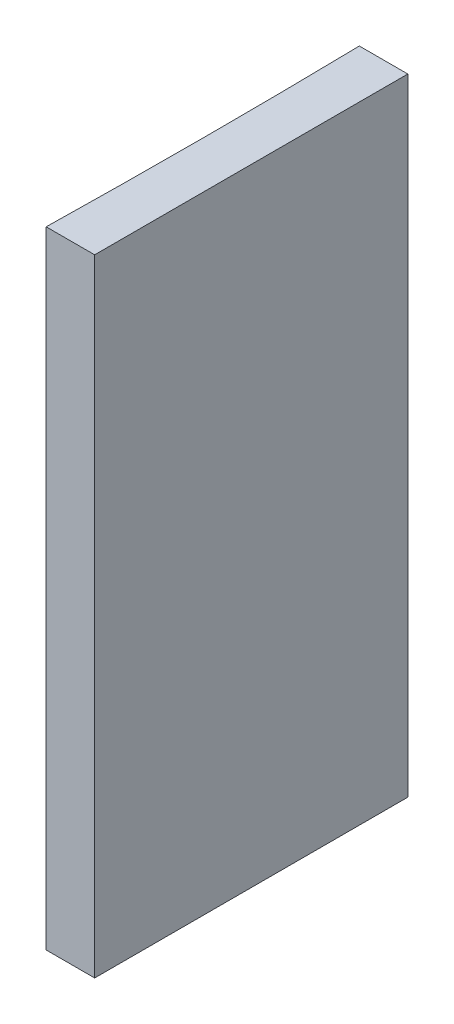
SolidWorks part; units mm, degrees
ref_plane "前视基准面" through (0, 0, 0) normal (0, 0, 1) x (1, 0, 0)
ref_plane "上视基准面" through (0, 0, 0) normal (0, 1, 0) x (1, 0, 0)
ref_plane "右视基准面" through (0, 0, 0) normal (1, 0, 0) x (0, 0, -1)
sketch "草图1" plane through (0, 0, 0) normal (0, 1, 0) x (1, 0, 0)
  line L0 (0, 0) -> (0, -20)
  line L1 (0, 0) -> (-3.0968, 0)
  line L2 (0, -20) -> (-3.0968, -20)
  line L3 (8.2336, -10) -> (-10.4405, -10) construction
  arc A0 (-3.0968, -20) -> (-3.0968, 0) centre (-519.8, -10) ccw
  point P7 (-3, -10)
  point P8 (0, -10)
  dimension "D2" = 516.8
  dimension "D3" = 3
  dimension "D1" = 20
extrude "凸台-拉伸1" add sketch "草图1" along normal blind 40
